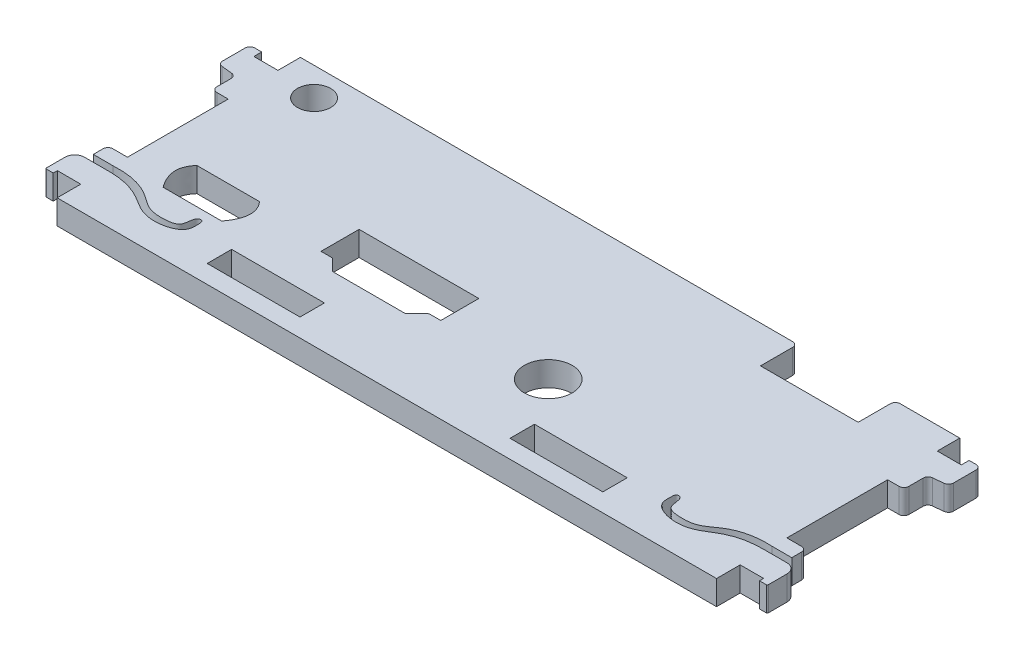
SolidWorks part; units mm, degrees
material "Custom Plastic"
ref_plane "Front Plane" through (0, 0, 0) normal (0, 0, 1) x (1, 0, 0)
ref_plane "Top Plane" through (0, 0, 0) normal (0, 1, 0) x (1, 0, 0)
ref_plane "Right Plane" through (0, 0, 0) normal (1, 0, 0) x (0, 0, -1)
sketch "Sketch1" plane through (0, 0, 0) normal (0, 1, 0) x (1, 0, 0)
  line L0 (34.4805, 15.1765) -> (34.4805, 10.9855)
  line L1 (-42.8625, -15.8115) -> (42.8625, -15.8115)
  line L2 (-42.8625, -15.8115) -> (-42.8625, -12.7381)
  line L3 (-42.8625, 15.8115) -> (21.1455, 15.8115)
  line L4 (42.8625, -15.8115) -> (42.8625, -12.7381)
  line L5 (-42.8625, -15.8115) -> (42.8625, 15.8115) construction
  line L6 (-42.8625, 15.8115) -> (42.8625, -15.8115) construction
  line L7 (34.4805, 10.9855) -> (21.7805, 10.9855)
  line L8 (21.7805, 10.9855) -> (21.7805, 15.1765)
  line L9 (35.1155, 15.8115) -> (42.8625, 15.8115)
  line L10 (13.6525, -10.2743) -> (13.6525, -13.4493)
  line L11 (13.6525, -13.4493) -> (25.7175, -13.4493)
  line L12 (25.7175, -13.4493) -> (25.7175, -10.2743)
  line L13 (25.7175, -10.2743) -> (13.6525, -10.2743)
  line L14 (0, 15.8115) -> (0, -15.8115) construction
  line L15 (-25.7175, -10.2743) -> (-13.6525, -10.2743)
  line L16 (-25.7175, -13.4493) -> (-25.7175, -10.2743)
  line L17 (-13.6525, -13.4493) -> (-25.7175, -13.4493)
  line L18 (-13.6525, -10.2743) -> (-13.6525, -13.4493)
  line L19 (42.8625, 12.8905) -> (45.9867, 12.8905)
  line L20 (45.9867, 12.8905) -> (45.9867, 13.9065)
  line L21 (45.9867, 13.9065) -> (46.8757, 13.9065)
  line L22 (47.5107, 13.2715) -> (47.5107, 10.3381)
  line L23 (46.9421, 9.7065) -> (45.5532, 9.5606)
  line L24 (44.9846, 8.929) -> (44.9846, 7.0624)
  line L25 (44.3496, 6.4274) -> (42.8625, 6.4274)
  line L26 (42.8625, 12.8905) -> (42.8625, 15.8115)
  line L27 (-44.3496, 6.4274) -> (-42.8625, 6.4274)
  line L28 (-42.8625, 12.8905) -> (-45.9867, 12.8905)
  line L29 (-44.9846, 8.929) -> (-44.9846, 7.0624)
  line L30 (-46.9421, 9.7065) -> (-45.5532, 9.5606)
  line L31 (-47.5107, 13.2715) -> (-47.5107, 10.3381)
  line L32 (-45.9867, 13.9065) -> (-46.8757, 13.9065)
  line L33 (-45.9867, 12.8905) -> (-45.9867, 13.9065)
  line L34 (-42.8625, 12.8905) -> (-42.8625, 15.8115)
  line L35 (-42.8625, -6.6675) -> (-44.7675, -6.6675)
  line L36 (-45.4025, -7.3025) -> (-45.4025, -8.5725)
  line L37 (-45.4025, -8.5725) -> (-42.8625, -8.5725)
  line L38 (-42.8625, -6.6675) -> (-42.8625, 6.4274)
  line L39 (-42.8625, -9.4615) -> (-45.4025, -9.4615)
  line L40 (-45.4025, -9.4615) -> (-45.6565, -9.4615)
  line L41 (-46.9265, -10.7315) -> (-46.9265, -13.1445)
  line L42 (-46.7995, -13.2715) -> (-45.9105, -13.2715)
  line L43 (-45.9105, -13.2715) -> (-45.9105, -12.7381)
  line L44 (-45.9105, -12.7381) -> (-42.8625, -12.7381)
  line L45 (45.9105, -12.7381) -> (42.8625, -12.7381)
  line L46 (45.9105, -13.2715) -> (45.9105, -12.7381)
  line L47 (46.7995, -13.2715) -> (45.9105, -13.2715)
  line L48 (46.9265, -10.7315) -> (46.9265, -13.1445)
  line L49 (45.4025, -9.4615) -> (45.6565, -9.4615)
  line L50 (42.8625, -9.4615) -> (45.4025, -9.4615)
  line L51 (45.4025, -8.5725) -> (42.8625, -8.5725)
  line L52 (45.4025, -7.3025) -> (45.4025, -8.5725)
  line L53 (42.8625, -6.6675) -> (44.7675, -6.6675)
  line L54 (42.8625, -6.6675) -> (42.8625, 6.4274)
  line L55 (-19.685, -13.4493) -> (-19.685, -7.2616) construction
  line L56 (-19.685, 0.2667) -> (-4.1148, 0.2667)
  line L57 (-4.1148, 0.2667) -> (-4.1148, -4.6863)
  line L58 (-4.1148, -4.6863) -> (-5.5336, -4.6863)
  line L59 (-5.7132, -4.7607) -> (-7.1628, -6.2103)
  line L60 (-7.1628, -6.2103) -> (-16.637, -6.2103)
  line L61 (-11.8999, 0.2667) -> (-11.8999, -6.2103) construction
  line L62 (-7.1628, -6.2103) -> (-3.803, -6.2103) construction
  line L63 (-16.637, -6.2103) -> (-19.9968, -6.2103) construction
  line L64 (-18.0866, -4.7607) -> (-16.637, -6.2103)
  line L65 (-19.685, -4.6863) -> (-18.2662, -4.6863)
  line L66 (-19.685, 0.2667) -> (-19.685, -4.6863)
  line L67 (-19.9968, -6.2103) -> (-41.2704, -6.2103) construction
  line L68 (-37.4142, -3.0855) -> (-29.2862, -3.0855)
  line L69 (-33.3502, -3.0855) -> (-33.3502, -7.7337) construction
  line L70 (-29.5402, -7.7337) -> (-37.1602, -7.7337)
  arc A0 (44.9846, 7.0624) -> (44.3496, 6.4274) centre (44.3496, 7.0624) cw
  arc A1 (44.9846, 8.929) -> (45.5532, 9.5606) centre (45.6196, 8.929) cw
  arc A2 (46.8757, 13.9065) -> (47.5107, 13.2715) centre (46.8757, 13.2715) cw
  arc A3 (47.5107, 10.3381) -> (46.9421, 9.7065) centre (46.8757, 10.3381) cw
  arc A4 (-44.9846, 7.0624) -> (-44.3496, 6.4274) centre (-44.3496, 7.0624) ccw
  arc A5 (-47.5107, 10.3381) -> (-46.9421, 9.7065) centre (-46.8757, 10.3381) ccw
  arc A6 (-46.8757, 13.9065) -> (-47.5107, 13.2715) centre (-46.8757, 13.2715) ccw
  arc A7 (-44.9846, 8.929) -> (-45.5532, 9.5606) centre (-45.6196, 8.929) ccw
  circle A8 centre (-37.4015, 12.1285) radius 2.159
  arc A9 (35.1155, 15.8115) -> (34.4805, 15.1765) centre (35.1155, 15.1765) ccw
  arc A10 (21.7805, 15.1765) -> (21.1455, 15.8115) centre (21.1455, 15.1765) ccw
  arc A11 (-45.6565, -9.4615) -> (-46.9265, -10.7315) centre (-45.6565, -10.7315) ccw
  arc A12 (-46.7995, -13.2715) -> (-46.9265, -13.1445) centre (-46.7995, -13.1445) cw
  arc A13 (-44.7675, -6.6675) -> (-45.4025, -7.3025) centre (-44.7675, -7.3025) ccw
  arc A14 (44.7675, -6.6675) -> (45.4025, -7.3025) centre (44.7675, -7.3025) cw
  arc A15 (46.7995, -13.2715) -> (46.9265, -13.1445) centre (46.7995, -13.1445) ccw
  arc A16 (45.6565, -9.4615) -> (46.9265, -10.7315) centre (45.6565, -10.7315) cw
  arc A17 (-18.2662, -4.6863) -> (-18.0866, -4.7607) centre (-18.2662, -4.9403) cw
  arc A18 (-5.5336, -4.6863) -> (-5.7132, -4.7607) centre (-5.5336, -4.9403) ccw
  circle A19 centre (9.4742, -4.3053) radius 3.1115
  spline S0 degree 3 poles (-42.8625, -8.5725) (-41.0051, -8.4665) (-38.396, -8.8878) (-35.8138, -11.1451) (-33.8394, -11.353) (-31.6872, -11.0943) (-31.6797, -9.7588) (-31.4293, -8.9527) (-30.7445, -8.8924) (-30.6816, -9.8708) (-30.7136, -11.4517) (-33.5253, -12.3771) (-36.0934, -11.8291) (-38.7927, -9.8264) (-41.2611, -9.4123) (-42.8625, -9.4615) knots 0 0 0 0 0.193262 0.266307 0.344937 0.408051 0.447196 0.474223 0.483837 0.508634 0.551486 0.654565 0.748054 0.830604 1 1 1 1
  spline S1 degree 3 poles (42.8625, -8.5725) (41.0051, -8.4665) (38.396, -8.8878) (35.8138, -11.1451) (33.8394, -11.353) (31.6872, -11.0943) (31.6797, -9.7588) (31.4293, -8.9527) (30.7445, -8.8924) (30.6816, -9.8708) (30.7136, -11.4517) (33.5253, -12.3771) (36.0934, -11.8291) (38.7927, -9.8264) (41.2611, -9.4123) (42.8625, -9.4615) knots 0 0 0 0 0.193262 0.266307 0.344937 0.408051 0.447196 0.474223 0.483837 0.508634 0.551486 0.654565 0.748054 0.830604 1 1 1 1
  spline S2 degree 2 poles (-29.2862, -3.0855) (-27.5216, -5.0144) (-29.5402, -7.7337) knots 0 0 0 1 1 1
  spline S3 degree 2 poles (-37.4142, -3.0855) (-39.1788, -5.0144) (-37.1602, -7.7337) knots 0 0 0 1 1 1
  point P0 (0, 0)
  point P30 (44.9846, 6.4274)
  point P33 (44.9846, 9.5008)
  point P36 (47.5107, 13.9065)
  point P39 (47.5107, 9.7663)
  point P56 (-47.5107, 9.7663)
  point P57 (-47.5107, 13.9065)
  point P58 (-44.9846, 9.5008)
  point P59 (-44.9846, 6.4274)
  point P64 (34.4805, 15.8115)
  point P67 (21.7805, 15.8115)
  point P89 (-46.9265, -9.4615)
  point P95 (-46.9265, -13.2715)
  point P101 (-45.4025, -6.6675)
  point P133 (45.4025, -6.6675)
  point P134 (46.9265, -13.2715)
  point P135 (46.9265, -9.4615)
  point P152 (-18.161, -4.6863)
  point P155 (-5.6388, -4.6863)
  dimension "D18" = 0.635
  dimension "D19" = 0.635
  dimension "D20" = 0.635
  dimension "D21" = 0.635
  dimension "D22" = 4.318
  dimension "D23" = 59.182
  dimension "D24" = 3.683
  dimension "D25" = 0.635
  dimension "D26" = 0.635
  dimension "D29" = 28.9258
  dimension "D30" = 28.9258
  dimension "D38" = 1.27
  dimension "D39" = 0.127
  dimension "D40" = 0.635
  dimension "D41" = 0.254
  dimension "D48" = 0.254
  dimension "D56" = 6.223
  dimension "D57" = 5.969
  dimension "D1" = 85.725
  dimension "D2" = 31.623
  dimension "D3" = 8.382
  dimension "D4" = 12.7
  dimension "D5" = 4.826
  dimension "D6" = 17.145
  dimension "D7" = 3.175
  dimension "D8" = 12.065
  dimension "D9" = 2.3622
  dimension "D10" = 2.921
  dimension "D11" = 1.016
  dimension "D12" = 1.524
  dimension "D13" = 4.1402
  dimension "D14" = 2.54
  dimension "D15" = 3.0734
  dimension "D16" = 3.1242
  dimension "D17" = 96
  dimension "D27" = 9.144
  dimension "D28" = 1.905
  dimension "D31" = 2.4449
  dimension "D32" = 2.54
  dimension "D33" = 4.064
  dimension "D34" = 3.81
  dimension "D35" = 1.016
  dimension "D36" = 0.5334
  dimension "D37" = 0.889
  dimension "D42" = 4.953
  dimension "D43" = 1.524
  dimension "D44" = 1.524
  dimension "D45" = 4.7371
  dimension "D46" = 45
  dimension "D47" = 4.064
  dimension "D49" = 9.0678
  dimension "D50" = 8.128
  dimension "D51" = 7.62
  dimension "D52" = 2.5406
  dimension "D53" = 4.6482
  dimension "D54" = 9.1948
  dimension "D55" = 13.589
extrude "Boss-Extrude1" add sketch "Sketch1" along normal blind 3.175
